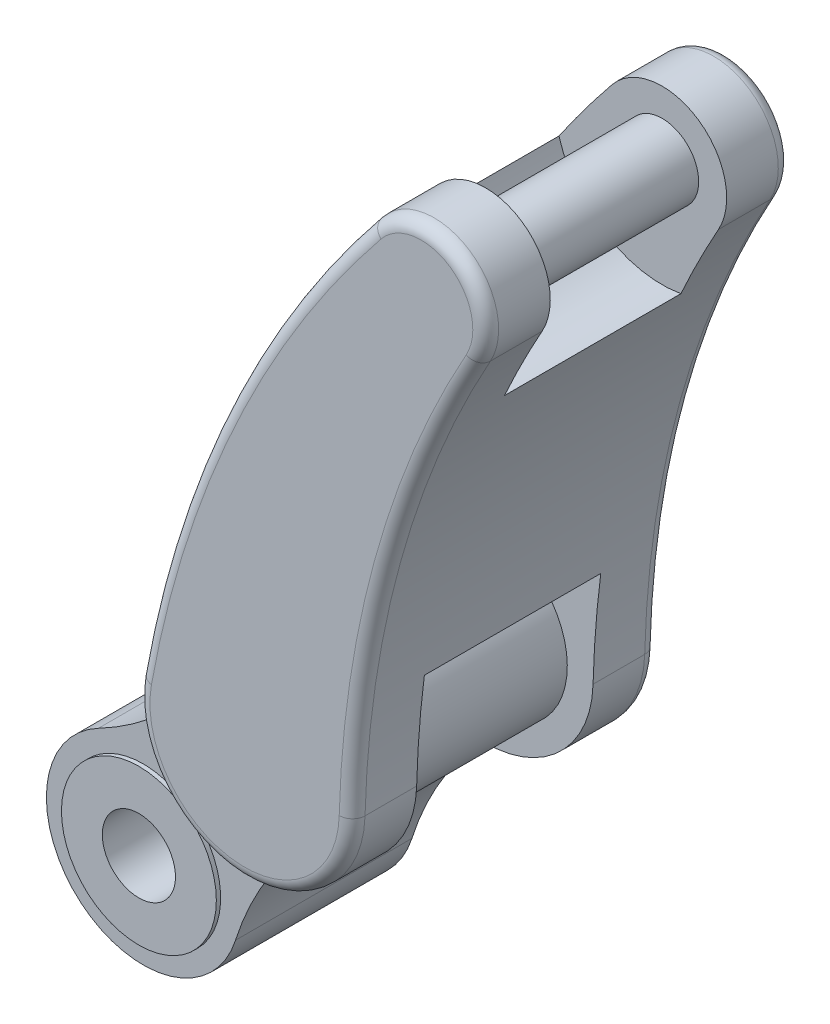
SolidWorks part; units mm, degrees
material "Balsa"
ref_plane "Front Plane" through (0, 0, 0) normal (0, 0, 1) x (1, 0, 0)
ref_plane "Top Plane" through (0, 0, 0) normal (0, 1, 0) x (1, 0, 0)
ref_plane "Right Plane" through (0, 0, 0) normal (1, 0, 0) x (0, 0, -1)
sketch "Sketch1" plane through (0, 0, 0) normal (0, 0, 1) x (1, 0, 0)
  line L0 (0, 0) -> (192.8363, 229.8133) construction
  line L1 (0, 0) -> (160.3767, 0) construction
  circle A0 centre (0, 0) radius 42.5
  arc A1 (-52.0686, 99.7252) -> (107.2517, -33.9605) centre (0, 0) ccw
  arc A2 (245.7988, 150.9465) -> (105.9708, 268.2761) centre (192.8363, 229.8133) ccw
  arc A3 (105.9708, 268.2761) -> (-52.0686, 99.7252) centre (-214.0599, 409.9812) cw
  arc A4 (107.2517, -33.9605) -> (245.7988, 150.9465) centre (440.9238, -139.6154) cw
  dimension "D1" = 85
  dimension "D2" = 225
  dimension "D5" = 190
  dimension "D6" = 350
  dimension "D7" = 350
  dimension "D3" = 50
  dimension "D4" = 300
extrude "Boss-Extrude1" add sketch "Sketch1" along normal mid plane 205
sketch "Sketch2" plane through (0, 0, 102.5) normal (0, 0, 1) x (1, 0, 0)
  circle A0 centre (0, 0) radius 90
  circle A1 centre (0, 0) radius 42.5 construction
  circle A2 centre (0, 0) radius 42.5
  dimension "D1" = 180
extrude "Boss-Extrude2" add sketch "Sketch2" along normal blind 5
sketch "Sketch3" plane through (0, 0, -102.5) normal (0, 0, -1) x (-1, 0, 0)
  circle A0 centre (0, 0) radius 42.5 construction
  circle A1 centre (0, 0) radius 90
  circle A2 centre (0, 0) radius 90
  circle A3 centre (0, 0) radius 42.5
  dimension "D1" = 0
extrude "Boss-Extrude3" add sketch "Sketch3" along normal blind 5
sketch "Sketch4" plane through (0, 0, 102.5) normal (0, 0, 1) x (1, 0, 0)
  line L0 (192.8363, 229.8133) -> (398.0484, 793.6289) construction
  line L1 (192.8363, 229.8133) -> (621.5615, 229.8133) construction
  arc A0 (245.7988, 150.9465) -> (105.9708, 268.2761) centre (192.8363, 229.8133) ccw construction
  arc A1 (245.7988, 150.9465) -> (105.9708, 268.2761) centre (192.8363, 229.8133) ccw construction
  arc A2 (69.8118, 251.9485) -> (317.8363, 229.8133) centre (192.8363, 229.8133) ccw
  arc A3 (463.5182, 757.0406) -> (339.8105, 840.8873) centre (398.0484, 793.6289) ccw
  arc A4 (69.8118, 251.9485) -> (339.8105, 840.8873) centre (1349.2668, 21.7426) cw
  arc A5 (317.7924, 226.5002) -> (463.5182, 757.0406) centre (1467.3884, 196.0195) cw
  dimension "D1" = 250
  dimension "D4" = 150
  dimension "D5" = 1150
  dimension "D6" = 1300
  dimension "D2" = 600
  dimension "D3" = 70
extrude "Boss-Extrude4" add sketch "Sketch4" along normal blind 75
sketch "Sketch5" plane through (0, 0, -102.5) normal (0, 0, -1) x (-1, 0, 0)
  arc A4 (-317.7924, 226.5002) -> (-69.8118, 251.9485) centre (-192.8363, 229.8133) ccw
  arc A5 (-317.7924, 226.5002) -> (-463.5182, 757.0406) centre (-1467.3884, 196.0195) ccw
  arc A6 (-339.8105, 840.8873) -> (-463.5182, 757.0406) centre (-398.0484, 793.6289) ccw
  arc A7 (-69.8118, 251.9485) -> (-339.8105, 840.8873) centre (-1349.2668, 21.7426) ccw
  arc A8 (-317.7924, 226.5002) -> (-69.8118, 251.9485) centre (-192.8363, 229.8133) ccw
  arc A9 (-317.7924, 226.5002) -> (-463.5182, 757.0406) centre (-1467.3884, 196.0195) ccw
  arc A10 (-339.8105, 840.8873) -> (-463.5182, 757.0406) centre (-398.0484, 793.6289) ccw
  arc A11 (-69.8118, 251.9485) -> (-339.8105, 840.8873) centre (-1349.2668, 21.7426) ccw
  dimension "D1" = 0
extrude "Boss-Extrude5" add sketch "Sketch5" along normal blind 75
fillet "Fillet2" radius 15 8 edges at (167.5346, 563.5073, 177.5) (440.1274, 855.7124, 177.5) (358.4599, 500.6136, 177.5) (180.0755, 105.4664, 177.5) (440.1274, 855.7124, -177.5) (167.5346, 563.5073, -177.5) (180.0755, 105.4664, -177.5) (358.4599, 500.6136, -177.5)
sketch "Sketch6" plane through (0, 0, -102.5) normal (0, 0, 1) x (1, 0, 0)
  circle A0 centre (398.0484, 793.6289) radius 42.5
  arc A1 (463.5182, 757.0406) -> (317.7924, 226.5002) centre (1467.3884, 196.0195) ccw construction
  arc A2 (339.8105, 840.8873) -> (69.8118, 251.9485) centre (1349.2668, 21.7426) ccw construction
  arc A3 (419.8557, 670.5458) -> (326.7517, 342.4707) centre (1467.3884, 196.0195) ccw
  arc A4 (278.1195, 758.386) -> (98.8783, 377.451) centre (1349.2668, 21.7426) ccw
  arc A5 (278.1195, 758.386) -> (419.8557, 670.5458) centre (398.0484, 793.6289) ccw
  arc A6 (326.7517, 342.4707) -> (98.8783, 377.451) centre (192.8363, 229.8133) ccw
  dimension "D1" = 85
  dimension "D2" = 250
  dimension "D3" = 350
extrude "Boss-Extrude6" add sketch "Sketch6" along normal up to surface (205 mm away) up to face at (234.2074, 369.5113, 102.5)
